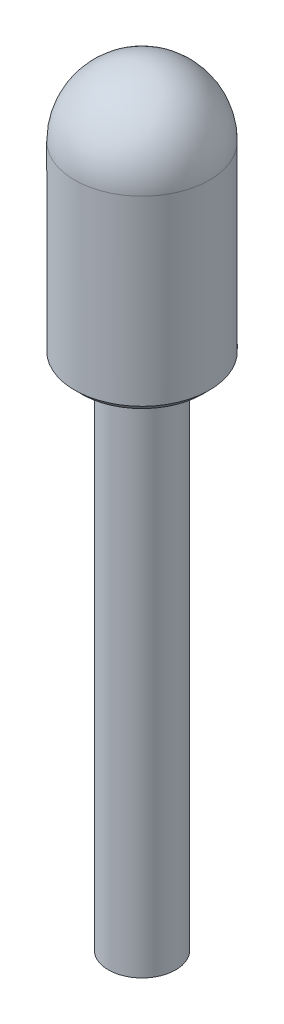
SolidWorks part; units mm, degrees
ref_plane "Front Plane" through (0, 0, 0) normal (0, 0, 1) x (1, 0, 0)
ref_plane "Top Plane" through (0, 0, 0) normal (0, 1, 0) x (1, 0, 0)
ref_plane "Right Plane" through (0, 0, 0) normal (1, 0, 0) x (0, 0, -1)
sketch "Sketch1" plane through (0, 0, 0) normal (0, 0, 1) x (1, 0, 0)
  line L0 (0, 0) -> (0, 11.8483) construction
  line L1 (0, 0) -> (0.5, 0)
  line L2 (0.5, 0) -> (0.5, 7.6)
  line L3 (0.5, 7.6) -> (1, 7.6)
  line L4 (1, 7.6) -> (1, 10.4)
  line L5 (0, 11.4) -> (0, 0)
  arc A0 (1, 10.4) -> (0, 11.4) centre (0, 10.4) ccw
  dimension "D1" = 1
  dimension "D2" = 2
  dimension "D3" = 11.4
  dimension "D4" = 7.6
revolve "Revolve1" add sketch "Sketch1" angle 360 about L0
chamfer "Chamfer1" distance 0.1 angle 45 1 edges at (0, 7.6, -1)
